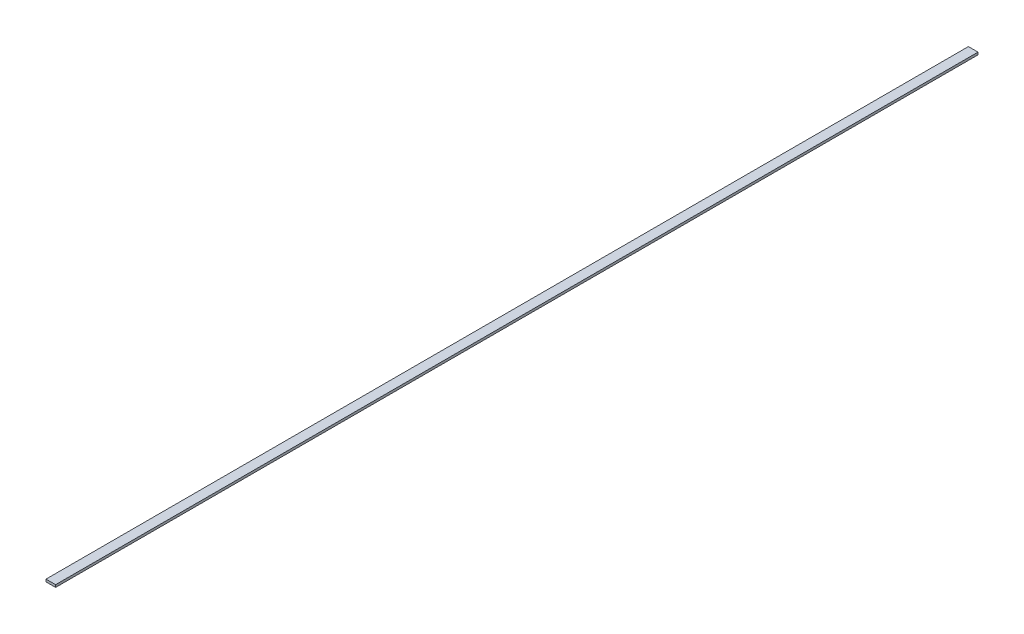
SolidWorks part; units mm, degrees
material "6061 Alloy"
ref_plane "Front" through (0, 0, 0) normal (0, 0, 1) x (1, 0, 0)
ref_plane "Top" through (0, 0, 0) normal (0, 1, 0) x (1, 0, 0)
ref_plane "Right" through (0, 0, 0) normal (1, 0, 0) x (0, 0, -1)
sketch "Sketch1" plane through (0, 0, 0) normal (0, 1, 0) x (1, 0, 0)
  line L1 (-6.35, -609.6) -> (6.35, -609.6)
  line L2 (-6.35, -609.6) -> (-6.35, 609.6)
  line L3 (-6.35, 609.6) -> (6.35, 609.6)
  line L4 (6.35, -609.6) -> (6.35, 609.6)
  line L5 (-6.35, -609.6) -> (6.35, 609.6) construction
  line L6 (-6.35, 609.6) -> (6.35, -609.6) construction
  point P0 (0, 0)
  dimension "D1" = 1219.2
  dimension "D2" = 12.7
extrude "Boss-Extrude1" add sketch "Sketch1" along normal mid plane 3.175
